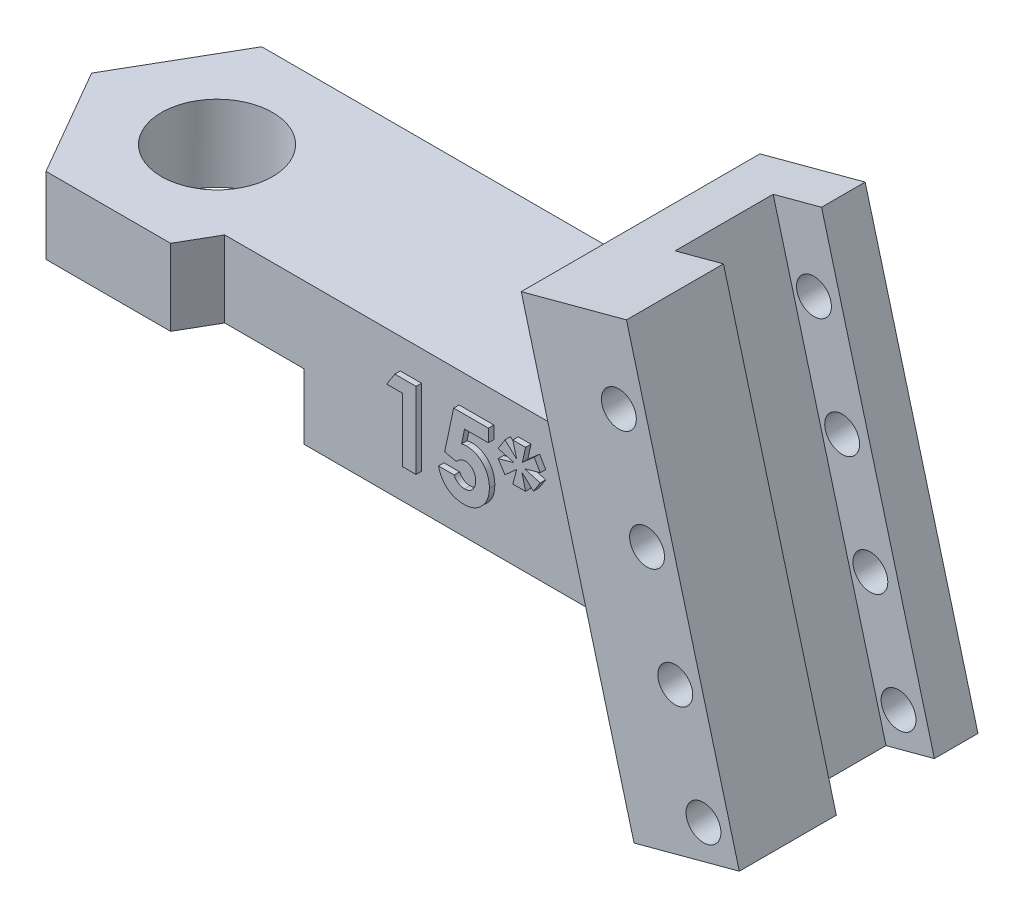
SolidWorks part; units mm, degrees
ref_plane "Front Plane" through (0, 0, 0) normal (0, 0, 1) x (1, 0, 0)
ref_plane "Top Plane" through (0, 0, 0) normal (0, 1, 0) x (1, 0, 0)
ref_plane "Right Plane" through (0, 0, 0) normal (1, 0, 0) x (0, 0, -1)
sketch "Sketch1" plane through (0, 0, 0) normal (0, 1, 0) x (1, 0, 0)
  line L1 (0, 0) -> (25, 0)
  line L2 (0, 0) -> (0, -6.75)
  line L3 (0, -6.75) -> (25, -6.75)
  line L4 (25, 0) -> (25, -6.75)
  dimension "D1" = 6.75
  dimension "D2" = 25
extrude "Boss-Extrude1" add sketch "Sketch1" along normal blind 6.5
ref_plane "Plane1" through (0, 0, 3.375) normal (0, 0, 1) x (1, 0, 0)
sketch "Sketch5" plane through (0, 6.5, 0) normal (0, 1, 0) x (1, 0, 0)
  line L0 (0, 0) -> (0, -6.75) construction
  line L1 (-5.7158, -3.375) -> (-2.8579, -8.325)
  line L2 (-2.8579, -8.325) -> (2.8579, -8.325)
  line L3 (2.8579, -8.325) -> (5.7158, -3.375)
  line L4 (5.7158, -3.375) -> (2.8579, 1.575)
  line L5 (2.8579, 1.575) -> (-2.8579, 1.575)
  line L6 (-2.8579, 1.575) -> (-5.7158, -3.375)
  circle A0 centre (0, -3.375) radius 4.95 construction
  dimension "D1" = 4.95
extrude "Boss-Extrude4" add sketch "Sketch5" against normal up to surface (6.5 mm away) up to face at (12.5, 0, 3.375)
sketch "Sketch3" plane through (0, 0, 3.375) normal (0, 0, 1) x (1, 0, 0)
  line L0 (19.994, 13.6715) -> (24.8236, 14.9656)
  line L1 (24.8236, 14.9656) -> (30, -4.353)
  line L2 (30, -4.353) -> (25.1704, -5.647)
  line L3 (25.1704, -5.647) -> (19.994, 13.6715)
  line L4 (3.7672, 6.5) -> (25, 6.5) construction
  point P6 (27.5852, -5)
  dimension "D1" = 30
  dimension "D2" = 5
  dimension "D3" = 20
  dimension "D4" = 75
  dimension "D6" = 5
extrude "Boss-Extrude3" add sketch "Sketch3" against normal up to surface (4.95 mm away) and the other way blind 6 up to face at (0, 3.25, -1.575)
sketch "Sketch4" plane through (-2.0785, 7.7572, 0) normal (-0.2588, 0.9659, 0) x (0.9659, 0.2588, 0)
  line L0 (27.8511, -9.375) -> (27.8511, 1.575) construction
  line L1 (25.5511, -0.425) -> (27.8511, -0.425)
  line L2 (25.5511, -0.425) -> (25.5511, -4.925)
  line L3 (25.5511, -4.925) -> (27.8511, -4.925)
  line L4 (27.8511, -0.425) -> (27.8511, -4.925)
  line L6 (27.8511, 1.575) -> (22.8511, 1.575) construction
  dimension "D1" = 4.5
  dimension "D2" = 2.3
  dimension "D3" = 2
extrude "Cut-Extrude1" cut sketch "Sketch4" against normal blind 23 contours L2 L3 L4 L1
sketch "Sketch6" plane through (0, 6.5, 0) normal (0, 1, 0) x (1, 0, 0)
  circle A0 centre (0, -3.3356) radius 2.55
  dimension "D1" = 5.1
extrude "Cut-Extrude2" cut sketch "Sketch6" against normal blind 10
sketch "Sketch7" plane through (0, 0, -1.575) normal (0, 0, -1) x (-1, 0, 0)
  line L0 (-2.8579, 0) -> (-23.6572, 0)
  line L1 (-23.6572, 0) -> (-25.1704, -5.647)
  line L2 (-25.1704, -5.647) -> (-30, -4.353)
  line L3 (-30, -4.353) -> (-24.8236, 14.9656)
  line L4 (-24.8236, 14.9656) -> (-19.994, 13.6715)
  line L5 (-19.994, 13.6715) -> (-21.9156, 6.5)
  line L6 (-21.9156, 6.5) -> (-2.8579, 6.5)
  line L7 (-2.8579, 6.5) -> (-2.8579, 0)
  dimension "D1" = 20
extrude "Boss-Extrude5" add sketch "Sketch7" against normal up to surface (1.575 mm away) up to face at (13.2768, 3.25, 0)
sketch "Sketch8" plane through (0, 0, 0) normal (0, -1, 0) x (-1, 0, 0)
  line L1 (-4.6765, -11.475) -> (4.6765, -11.475)
  line L2 (4.6765, -11.475) -> (9.3531, -3.375)
  line L3 (9.3531, -3.375) -> (4.6765, 4.725)
  line L4 (4.6765, 4.725) -> (-4.6765, 4.725)
  line L5 (-4.6765, 4.725) -> (-9.3531, -3.375)
  line L6 (-9.3531, -3.375) -> (-4.6765, -11.475)
  circle A0 centre (0, -3.375) radius 8.1 construction
  dimension "D1" = 16.2
extrude "Cut-Extrude3" cut sketch "Sketch8" against normal blind 3
sketch "Sketch9" plane through (0, 0, -1.575) normal (0, 0, -1) x (-1, 0, 0)
  line L0 (-30, -4.353) -> (-24.8236, 14.9656) construction
  line L1 (-25.1704, -5.647) -> (-30, -4.353) construction
  line L2 (-28.3561, -3.2405) -> (-24.4738, 11.2484) construction
  line L3 (-30, -4.353) -> (-24.8236, 14.9656) construction
  circle A0 centre (-28.3561, -3.2405) radius 0.8
  circle A4 centre (-27.062, 1.5891) radius 0.8
  circle A5 centre (-25.7679, 6.4187) radius 0.8
  circle A6 centre (-24.4738, 11.2484) radius 0.8
  point P6 (0, 0)
  point P7 (0, 0)
  point P14 (0, 0)
  point P15 (-25.5861, 11.3628)
  dimension "D1" = 1.6
  dimension "D2" = 1.3
  dimension "D5" = 5
  dimension "D3" = 1.5
  dimension "D4" = 5
  dimension "D6" = 5
extrude "Cut-Extrude4" cut sketch "Sketch9" against normal up to surface (10.95 mm away) up to face at (24.997, 4.6593, 9.375)
sketch "Sketch10" plane through (0, 0, 6.75) normal (0, 0, 1) x (1, 0, 0)
  text T0 "<b>15*</b>"
extrude "Boss-Extrude6" add sketch "Sketch10" along normal blind 0.25
